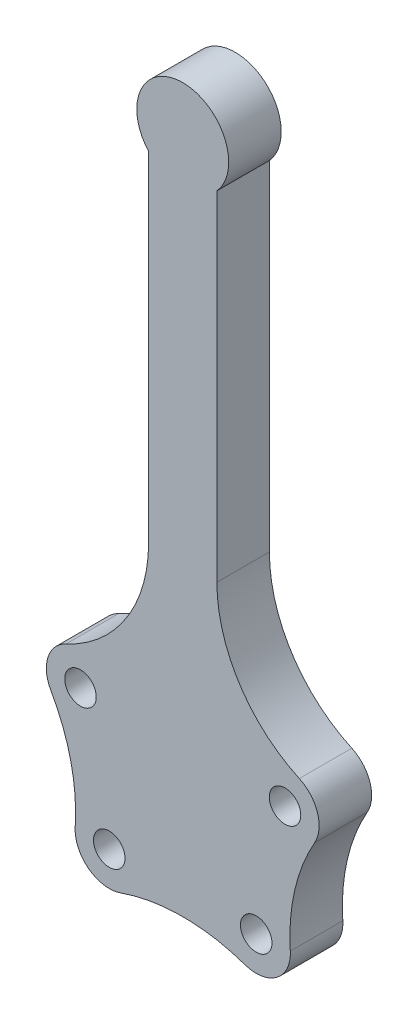
SolidWorks part; units mm, degrees
ref_plane "Front Plane" through (0, 0, 0) normal (0, 0, 1) x (1, 0, 0)
ref_plane "Top Plane" through (0, 0, 0) normal (0, 1, 0) x (1, 0, 0)
ref_plane "Right Plane" through (0, 0, 0) normal (1, 0, 0) x (0, 0, -1)
sketch "Sketch1" plane through (0, 0, 0) normal (0, 0, 1) x (1, 0, 0)
  line L0 (11000, 0) -> (-11000, 0) construction
  line L4 (12998.8492, 81173.1848) -> (12998.8492, 210284.6255)
  line L5 (-13001.1508, 81173.1848) -> (-13001.1508, 210284.6255)
  circle A0 centre (-1.1508, 0) radius 26000
  circle A2 centre (-1.1508, 0) radius 31500
  circle A3 centre (-27987.4416, -27359.918) radius 6000
  circle A4 centre (27985.1401, -27359.918) radius 6000
  circle A5 centre (-38950.495, 20327.8012) radius 6000
  circle A6 centre (38948.1934, 20327.8012) radius 6000
  circle A7 centre (-1.1508, 222000) radius 12000
  circle A8 centre (-1.1508, 222000) radius 17500
  arc A9 (-44393.1595, 32133.6219) -> (-50245.4913, 13891.7265) centre (-38950.495, 20327.8012) ccw
  arc A13 (-44393.1595, 32133.6219) -> (-13001.1508, 81173.1848) centre (-67001.1508, 81173.1848) ccw
  arc A14 (44390.858, 32133.6219) -> (12998.8492, 81173.1848) centre (66998.8492, 81173.1848) cw
  arc A15 (-40959.1403, -26502.5767) -> (-50245.4913, 13891.7265) centre (-112802.3944, -21754.2253) ccw
  arc A16 (40956.8387, -26502.5767) -> (50243.1898, 13891.7265) centre (112800.0928, -21754.2253) cw
  arc A17 (23704.8838, -39635.072) -> (-23707.1854, -39635.072) centre (-1.1508, -107620.5405) ccw
  arc A18 (-40959.1403, -26502.5767) -> (-23707.1854, -39635.072) centre (-27987.4416, -27359.918) ccw
  arc A19 (40956.8387, -26502.5767) -> (23704.8838, -39635.072) centre (27985.1401, -27359.918) cw
  arc A21 (44390.858, 32133.6219) -> (50243.1898, 13891.7265) centre (38948.1934, 20327.8012) cw
extrude "Boss-Extrude2" add sketch "Sketch1" along normal blind 20000 contours A21 A14 L4 A8 L5 A13 A9 A15 A18 A17 A19 A16 A2 A3 A4 A5 A6
